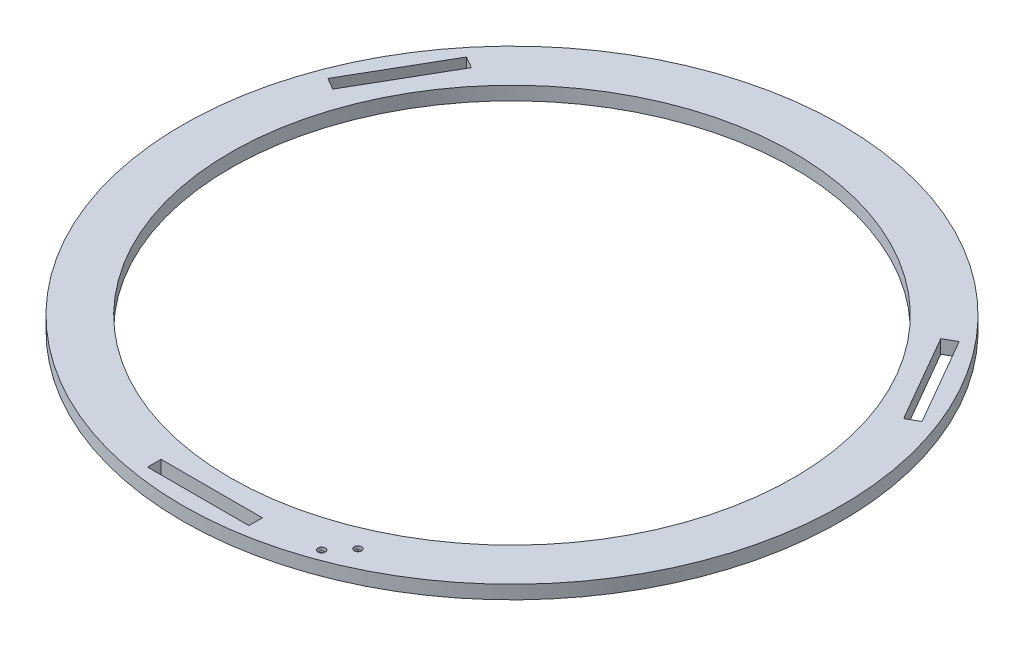
SolidWorks part; units mm, degrees
ref_plane "Front Plane" through (0, 0, 0) normal (0, 0, 1) x (1, 0, 0)
ref_plane "Top Plane" through (0, 0, 0) normal (0, 1, 0) x (1, 0, 0)
ref_plane "Right Plane" through (0, 0, 0) normal (1, 0, 0) x (0, 0, -1)
sketch "Sketch1" plane through (0, 0, 0) normal (0, 1, 0) x (1, 0, 0)
  circle A0 centre (0, 0) radius 250
  circle A1 centre (0, 0) radius 292.5
  dimension "D1" = 500
  dimension "D2" = 585
extrude "Boss-Extrude1" add sketch "Sketch1" along normal blind 12
sketch "Sketch2" plane through (0, 12, 0) normal (0, 1, 0) x (1, 0, 0)
  line L0 (-45, -278.5) -> (45, -278.5)
  line L1 (45, -278.5) -> (45, -266.5)
  line L2 (45, -266.5) -> (-45, -266.5)
  line L3 (-45, -266.5) -> (-45, -278.5)
  line L4 (0, -266.5) -> (0, 0) construction
  line L5 (0, -266.5) -> (0, -291) construction
  circle A0 centre (0, 0) radius 291 construction
  dimension "D4" = 582
  dimension "D1" = 12
  dimension "D2" = 90
  dimension "D3" = 12.5
extrude "Cut-Extrude1" cut sketch "Sketch2" against normal blind 12
pattern_circular "CirPattern1" count 3 over 360 about axis through (0, 0, 0) along (0, 1, 0) of "Cut-Extrude1"
hole_wizard "CBORE for M3 SHCS1" positions "Sketch5" profile "Sketch6" counterbore size "M3" standard "ANSI Metric" end condition through all
sketch "Sketch5" plane through (0, 12, 0) normal (0, 1, 0) x (1, 0, 0)
  point P0 (111.1755, -247.9405)
  point P2 (96.082, -265.0397)
sketch "Sketch6" plane through (111.1755, 12, 247.9405) normal (1, 0, 0) x (0, 0, 1)
  line L0 (0, 0) -> (0, 12)
  line L1 (0, 12) -> (1.7, 12)
  line L2 (1.7, 12) -> (1.7, 3)
  line L3 (1.7, 3) -> (3.25, 3)
  line L4 (3.25, 3) -> (3.25, 0)
  line L5 (3.25, 0) -> (0, 0)
  line L6 (0, -6.35) -> (0, 107.95) construction
  dimension "Thru Hole Dia." = 3.4
  dimension "Thru Hole Depth" = 12
  dimension "C'Bore Dia." = 6.5
  dimension "C'Bore Depth" = 3
